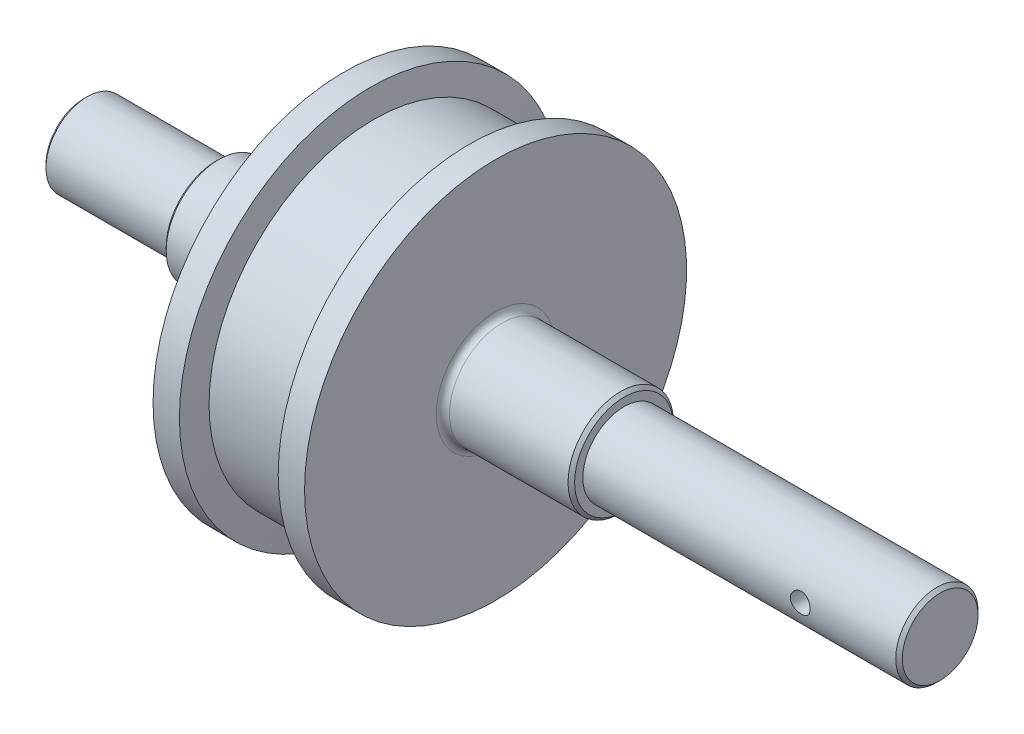
SolidWorks part; units mm, degrees
material "AISI 1045 钢，冷拔"
ref_plane "前视基准面" through (0, 0, 0) normal (0, 0, 1) x (1, 0, 0)
ref_plane "上视基准面" through (0, 0, 0) normal (0, 1, 0) x (1, 0, 0)
ref_plane "右视基准面" through (0, 0, 0) normal (1, 0, 0) x (0, 0, -1)
sketch "草图1" plane through (0, 0, 0) normal (0, 0, 1) x (1, 0, 0)
  line L0 (0, 0) -> (260, 0) construction
  line L1 (41, 16) -> (77, 16)
  line L2 (164, 15) -> (164, 12.5)
  line L3 (164, 12.5) -> (259, 12.5)
  line L4 (40, 15) -> (40, 12.5)
  line L5 (40, 12.5) -> (1, 12.5)
  line L6 (79, 18) -> (79, 58)
  line L7 (79, 58) -> (87, 58)
  line L8 (87, 58) -> (88, 50)
  line L9 (88, 50) -> (116, 50)
  line L10 (116, 50) -> (117, 58)
  line L11 (117, 58) -> (125, 58)
  line L12 (125, 58) -> (125, 18)
  line L13 (127, 16) -> (163, 16)
  line L14 (0, 0) -> (0, 11.5)
  line L15 (260, 0) -> (260, 11.5)
  line L16 (0, 11.5) -> (1, 12.5)
  line L17 (40, 15) -> (41, 16)
  line L18 (163, 16) -> (164, 15)
  line L19 (260, 11.5) -> (259, 12.5)
  line L20 (0, 0) -> (260, 0)
  arc A0 (125, 18) -> (127, 16) centre (127, 18) ccw
  arc A1 (79, 18) -> (77, 16) centre (77, 18) cw
  point P3 (40, 16)
  point P5 (164, 16)
  point P11 (260, 12.5)
  point P18 (0, 12.5)
  point P27 (125, 16)
  dimension "D16" = 2
  dimension "D1" = 124
  dimension "D2" = 8
  dimension "D3" = 8
  dimension "D4" = 50
  dimension "D5" = 28
  dimension "D6" = 8
  dimension "D7" = 8
  dimension "D8" = 9
  dimension "D9" = 9
  dimension "D10" = 39
  dimension "D11" = 12.5
  dimension "D12" = 12.5
  dimension "D13" = 16
  dimension "D14" = 40
  dimension "D15" = 260
revolve "旋转1" add sketch "草图1" angle 360 about L0
sketch "草图2" plane through (0, 0, 0) normal (0, 0, 1) x (1, 0, 0)
  line L0 (260, -11.5) -> (260, 11.5) construction
  circle A0 centre (230, 0) radius 3
  dimension "D1" = 30
  dimension "D2" = 6
extrude "切除-拉伸1" cut sketch "草图2" against normal mid plane 30 contours A0
